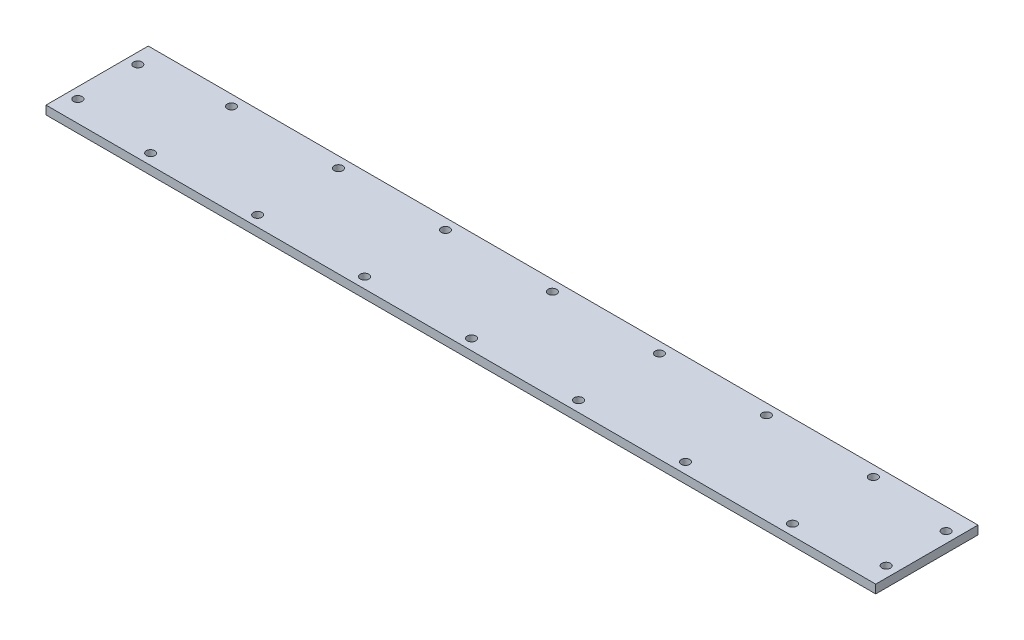
SolidWorks part; units mm, degrees
material "ABS PC"
ref_plane "Front Plane" through (0, 0, 0) normal (0, 0, 1) x (1, 0, 0)
ref_plane "Top Plane" through (0, 0, 0) normal (0, 1, 0) x (1, 0, 0)
ref_plane "Right Plane" through (0, 0, 0) normal (1, 0, 0) x (0, 0, -1)
sketch "Sketch1" plane through (0, 0, 0) normal (0, 1, 0) x (1, 0, 0)
  line L0 (0, 0) -> (-12.8519, 0) construction
  line L1 (-96.95, -11.95) -> (96.95, -11.95)
  line L2 (-96.95, -11.95) -> (-96.95, 11.95)
  line L3 (-96.95, 11.95) -> (96.95, 11.95)
  line L4 (96.95, -11.95) -> (96.95, 11.95)
  line L5 (-96.95, -11.95) -> (96.95, 11.95) construction
  line L6 (-96.95, 11.95) -> (96.95, -11.95) construction
  line L7 (0, 0) -> (0, 4.7059) construction
  circle A0 centre (-25, 9.45) radius 1
  circle A1 centre (0, 9.45) radius 1
  circle A2 centre (25, 9.45) radius 1
  circle A3 centre (-94.45, 7) radius 1
  circle A4 centre (25, -9.45) radius 1
  circle A5 centre (0, -9.45) radius 1
  circle A6 centre (-25, -9.45) radius 1
  circle A7 centre (-94.45, -7) radius 1
  circle A8 centre (94.45, -7) radius 1
  circle A9 centre (94.45, 7) radius 1
  circle A10 centre (-50, 9.45) radius 1
  circle A11 centre (-75, 9.45) radius 1
  circle A12 centre (75, 9.45) radius 1
  circle A13 centre (50, 9.45) radius 1
  circle A14 centre (75, -9.45) radius 1
  circle A15 centre (50, -9.45) radius 1
  circle A16 centre (-50, -9.45) radius 1
  circle A17 centre (-75, -9.45) radius 1
  point P0 (0, 0)
  point P29 (0, 0)
  dimension "D3" = 2
  dimension "D4" = 25
  dimension "D5" = 25
  dimension "D6" = 2.5
  dimension "D7" = 2.5
  dimension "D8" = 7
  dimension "D9" = 2
  dimension "D1" = 23.9
  dimension "D2" = 193.9
  dimension "D10" = 3
extrude "Boss-Extrude1" add sketch "Sketch1" along normal blind 2
